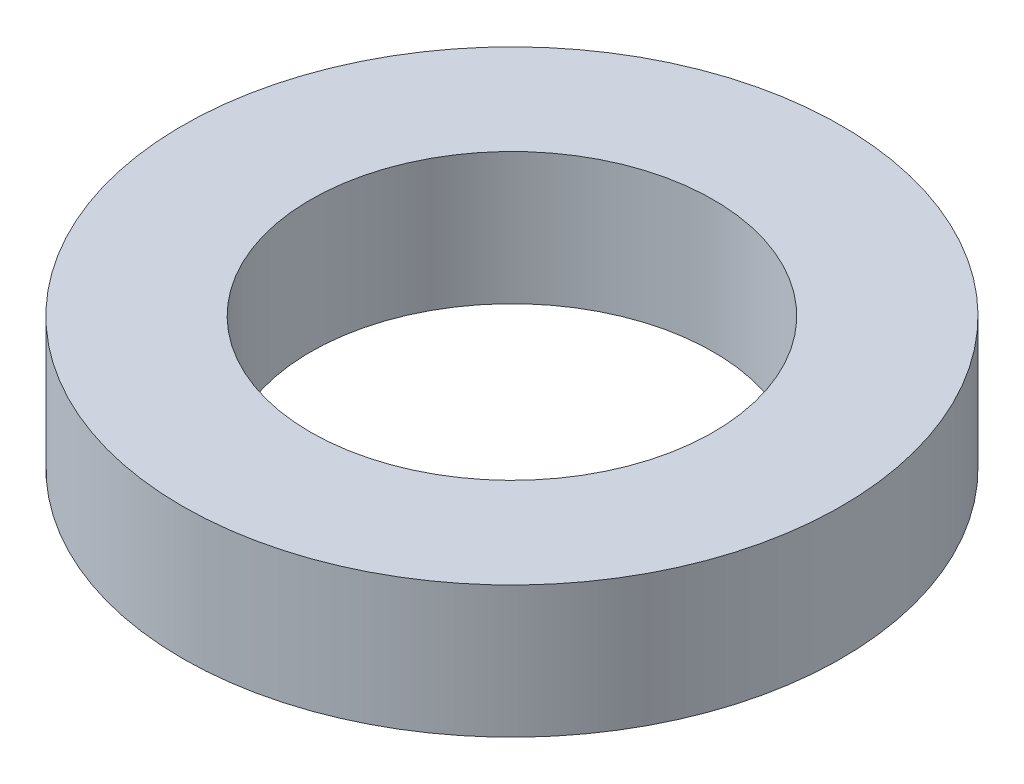
SolidWorks part; units mm, degrees
ref_plane "Front Plane" through (0, 0, 0) normal (0, 0, 1) x (1, 0, 0)
ref_plane "Top Plane" through (0, 0, 0) normal (0, 1, 0) x (1, 0, 0)
ref_plane "Right Plane" through (0, 0, 0) normal (1, 0, 0) x (0, 0, -1)
sketch "Sketch1" plane through (0, 0, 0) normal (0, 1, 0) x (1, 0, 0)
  circle A0 centre (0, 0) radius 45
  circle A1 centre (0, 0) radius 27.5
  point P19 (-12.3494, -9.4573)
  dimension "D1" = 55
  dimension "D2" = 90
extrude "Boss-Extrude1" add sketch "Sketch1" along normal blind 18
